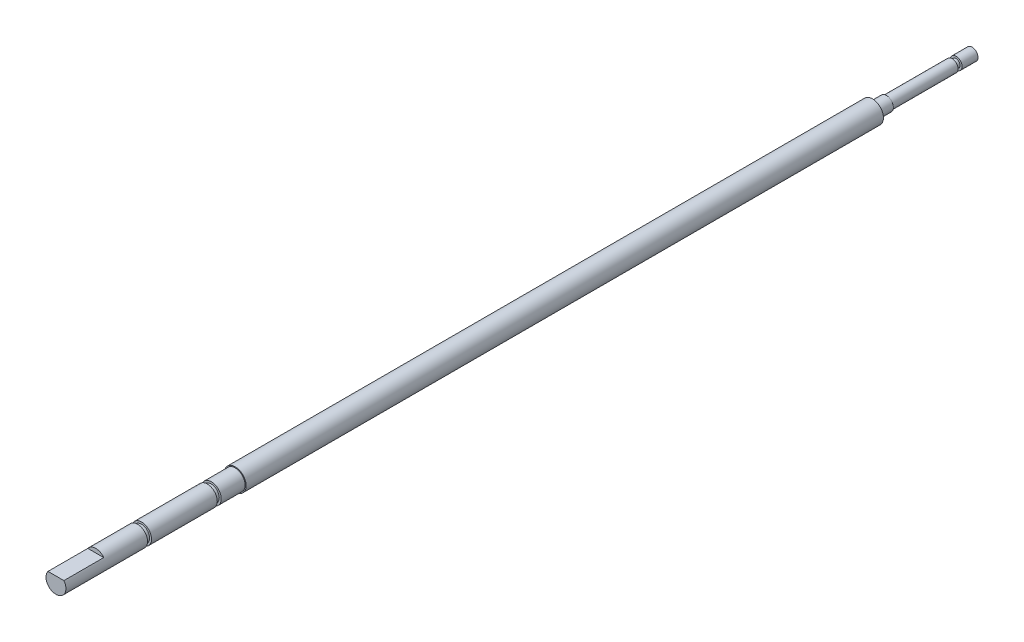
SolidWorks part; units mm, degrees
ref_plane "前视基准面" through (0, 0, 0) normal (0, 0, 1) x (1, 0, 0)
ref_plane "上视基准面" through (0, 0, 0) normal (0, 1, 0) x (1, 0, 0)
ref_plane "右视基准面" through (0, 0, 0) normal (1, 0, 0) x (0, 0, -1)
sketch "草图1" plane through (0, 0, 0) normal (0, 0, 1) x (1, 0, 0)
  circle A0 centre (0, 0) radius 2.75
  dimension "D1" = 5.5
extrude "凸台-拉伸6" add sketch "草图1" along normal blind 250 contours A0
cosmetic thread "装饰螺纹线23" parameters "D1"=155.5, "D2"=4.134
sketch "草图22" plane through (0, 0, 0) normal (0, 0, -1) x (-1, 0, 0)
  circle A0 centre (0, 0) radius 3.5433
  circle A1 centre (0, 0) radius 1.75
  dimension "D1" = 3.5
extrude "切除-拉伸16" cut sketch "草图22" against normal blind 25
ref_plane "基准面11" through (0, 0, 190) normal (0, 0, -1) x (-1, 0, 0)
sketch "草图23" plane through (0, 0, 190) normal (0, 0, -1) x (-1, 0, 0)
  circle A0 centre (0, 0) radius 4.9067
  circle A1 centre (0, 0) radius 2.5
  dimension "D1" = 5
extrude "切除-拉伸17" cut sketch "草图23" against normal through all
ref_plane "基准面12" through (0, 0, 193) normal (0, 0, -1) x (-1, 0, 0)
ref_plane "基准面13" through (0, 0, 212) normal (0, 0, 1) x (1, 0, 0)
sketch "草图29" plane through (0, 0, 250) normal (0, 0, 1) x (1, 0, 0)
  circle A0 centre (0, 0) radius 7.2245
extrude "切除-拉伸18" cut sketch "草图29" against normal blind 10
sketch "草图30" plane through (0, 0, 193) normal (0, 0, -1) x (-1, 0, 0)
  circle A0 centre (0, 0) radius 2.25
  dimension "D1" = 4.5
sketch "草图32" plane through (0, 0, 240) normal (0, 0, 1) x (1, 0, 0)
  line L0 (-2.25, 0) -> (2.25, 0) construction
  line L5 (-2, 1.5) -> (2, 1.5)
  circle A0 centre (0, 0) radius 2.25 construction
  circle A1 centre (0, 0) radius 2.5 construction
  arc A2 (2, 1.5) -> (-2, 1.5) centre (0, 0) ccw
  dimension "D2" = 1
extrude "切除-拉伸19" cut sketch "草图32" against normal blind 20
sketch "草图33" plane through (0, 0, 190) normal (0, 0, 1) x (1, 0, 0)
  circle A0 centre (0, 0) radius 3.4932
  circle A1 centre (0, 0) radius 2.5
  dimension "D1" = 5
extrude "切除-拉伸20" cut sketch "草图33" against normal blind 5
sketch "草图34" plane through (0, 0, 0) normal (0, 0, -1) x (-1, 0, 0)
  circle A0 centre (0, 0) radius 3.7837
  circle A1 centre (0, 0) radius 1.5
  dimension "D1" = 3
extrude "切除-拉伸21" cut sketch "草图34" against normal offset from surface (21.5 mm away) 3.5 up to face at (-1.75, 0, 25)
ref_plane "基准面14" through (0, 0, 5) normal (0, 0, -1) x (-1, 0, 0)
sketch "草图36" plane through (0, 0, 5) normal (0, 0, -1) x (-1, 0, 0)
  circle A0 centre (0, 0) radius 1
  circle A1 centre (0, 0) radius 3.5474
  circle A2 centre (0, 0) radius 1.5 construction
  dimension "D1" = 0.5
extrude "切除-拉伸22" cut sketch "草图36" along normal blind 1
ref_plane "基准面15" through (0, 0, 191) normal (0, 0, 1) x (1, 0, 0)
sketch "草图37" plane through (0, 0, 191) normal (0, 0, 1) x (1, 0, 0)
  circle A0 centre (0, 0) radius 5.0222
  circle A1 centre (0, 0) radius 2
  dimension "D1" = 4
extrude "切除-拉伸23" cut sketch "草图37" along normal blind 1
ref_plane "基准面16" through (0, 0, 208.5) normal (0, 0, 1) x (1, 0, 0)
sketch "草图38" plane through (0, 0, 208.5) normal (0, 0, 1) x (1, 0, 0)
  circle A0 centre (0, 0) radius 5.1601
  circle A1 centre (0, 0) radius 2
  dimension "D1" = 4
extrude "切除-拉伸24" cut sketch "草图38" along normal blind 1
sketch "草图39" plane through (0, 0, 240) normal (0, 0, 1) x (1, 0, 0)
  circle A0 centre (0, 0) radius 4.4659
extrude "切除-拉伸25" cut sketch "草图39" against normal blind 10
